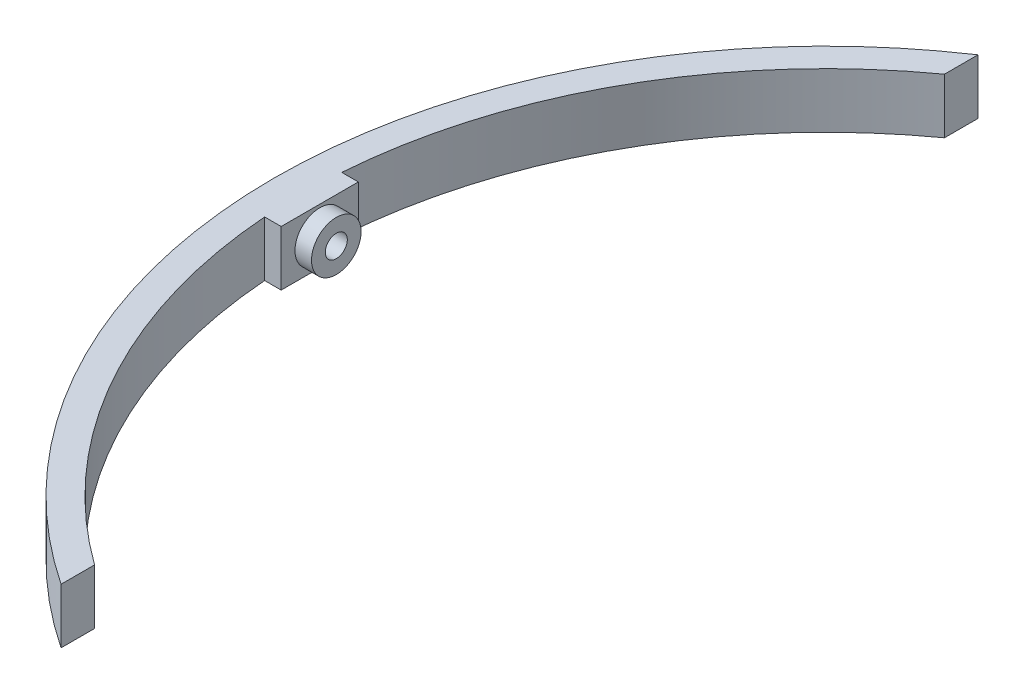
SolidWorks part; units mm, degrees
ref_plane "Спереди" through (0, 0, 0) normal (0, 0, 1) x (1, 0, 0)
ref_plane "Сверху" through (0, 0, 0) normal (0, 1, 0) x (1, 0, 0)
ref_plane "Справа" through (0, 0, 0) normal (1, 0, 0) x (0, 0, -1)
sketch "Sketch1" plane through (0, 0, 0) normal (0, 1, 0) x (1, 0, 0)
  line L0 (-55.4979, -83.1865) -> (-55.4979, -77.1037)
  line L1 (-55.4979, 77.1037) -> (-55.4979, 83.1865)
  line L4 (-94.7421, 6.9952) -> (-91.7421, 6.9952)
  line L5 (-91.7421, 6.9952) -> (-91.7421, -7.0048)
  line L6 (-91.7421, -7.0048) -> (-94.7414, -7.0048)
  line L8 (-94.038, 6.9952) -> (-94.7421, 6.9952)
  arc A0 (-55.4979, 77.1037) -> (-55.4979, -77.1037) centre (0, 0) ccw
  arc A1 (-55.4979, 83.1865) -> (-55.4979, -83.1865) centre (0, 0) ccw
extrude "Boss-Extrude1" add sketch "Sketch1" along normal blind 10 contours L1 A1 L0 A0 | L4 A0 L6 L5
ref_plane "Plane1" through (-91.7421, 0, 0) normal (1, 0, 0) x (0, 0, -1)
sketch "Sketch2" plane through (-91.7421, 0, 0) normal (1, 0, 0) x (0, 0, -1)
  circle A0 centre (0, 4.9384) radius 2
  circle A1 centre (0, 4.9384) radius 4.5
extrude "Boss-Extrude2" add sketch "Sketch2" along normal blind 3
sketch "Sketch3" plane through (-91.7421, 0, 0) normal (1, 0, 0) x (0, 0, -1)
  circle A0 centre (0, 4.9384) radius 2
extrude "Cut-Extrude1" cut sketch "Sketch3" against normal blind 10
